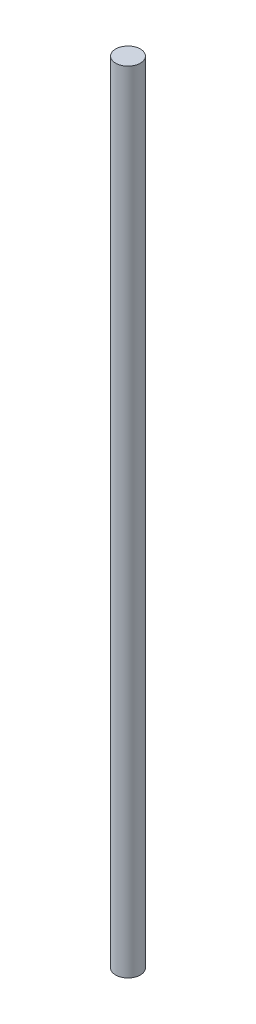
SolidWorks part; units mm, degrees
ref_plane "Front Plane" through (0, 0, 0) normal (0, 0, 1) x (1, 0, 0)
ref_plane "Top Plane" through (0, 0, 0) normal (0, 1, 0) x (1, 0, 0)
ref_plane "Right Plane" through (0, 0, 0) normal (1, 0, 0) x (0, 0, -1)
sketch "Sketch1" plane through (0, 0, 0) normal (0, 1, 0) x (1, 0, 0)
  circle A0 centre (0, 0) radius 2.3813
  dimension "D1" = 4.7625
extrude "Boss-Extrude1" add sketch "Sketch1" along normal blind 152.4
